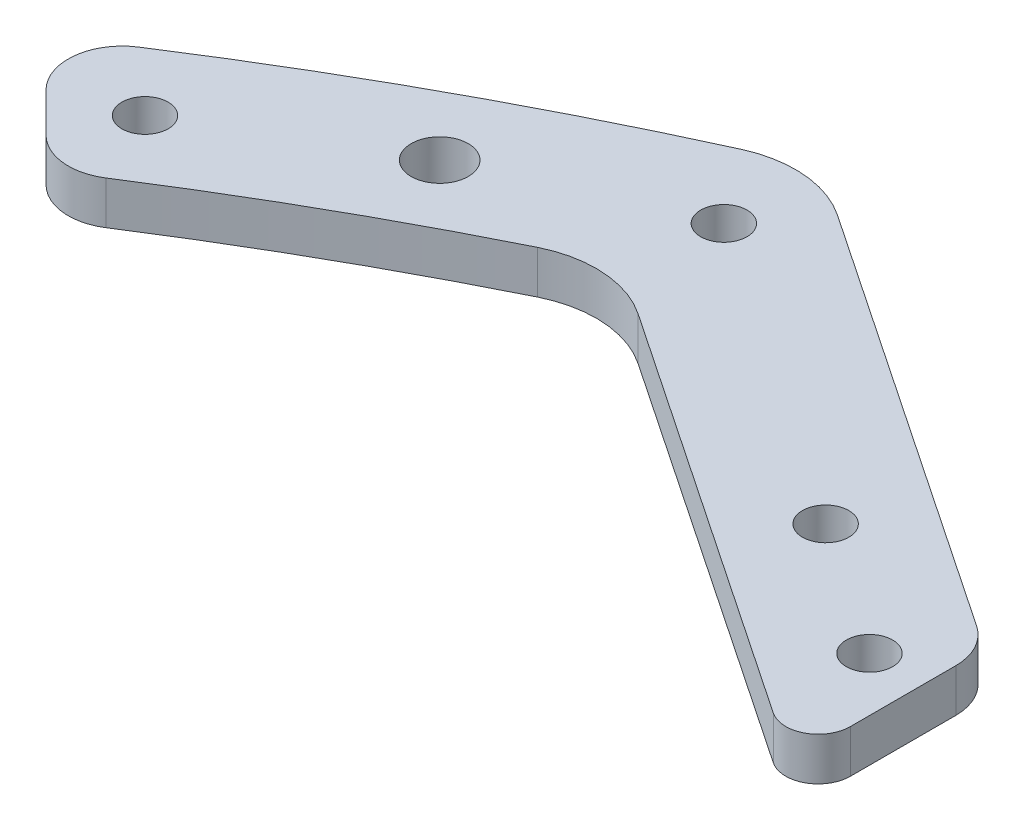
SolidWorks part; units mm, degrees
material "A-玻璃纤维"
ref_plane "前视基准面" through (0, 0, 0) normal (0, 0, 1) x (1, 0, 0)
ref_plane "上视基准面" through (0, 0, 0) normal (0, 1, 0) x (1, 0, 0)
ref_plane "右视基准面" through (0, 0, 0) normal (1, 0, 0) x (0, 0, -1)
sketch "草图1" plane through (0, 0, 0) normal (0, 1, 0) x (1, 0, 0)
  line L0 (0, 0) -> (275, 0) construction
  line L1 (0, 0) -> (0, 275) construction
  line L2 (0, 0) -> (194.4544, 194.4544) construction
  circle A0 centre (0, 0) radius 255
  circle A1 centre (0, 0) radius 275
  dimension "D1" = 510
  dimension "D2" = 20
  dimension "D3" = 45
extrude "凸台-拉伸1" add sketch "草图1" along normal blind 10
sketch "草图2" plane through (0, 10, 0) normal (0, 1, 0) x (1, 0, 0)
  line L0 (0, 0) -> (275, 0) construction
  line L1 (164.7559, 164.7559) -> (217.7889, 111.7229) construction
  line L2 (164.7559, 164.7559) -> (111.7229, 217.7889) construction
  line L3 (0, 0) -> (164.7559, 164.7559) construction
  line L4 (111.7229, 217.7889) -> (121.6224, 227.6884) construction
  line L5 (217.7889, 111.7229) -> (227.6884, 121.6224) construction
  line L6 (0, 0) -> (240.1716, 111.9938) construction
  line L7 (0, 0) -> (111.9938, 240.1716) construction
  line L8 (0, 0) -> (0, 275) construction
  line L9 (0, 185) -> (30, 185)
  line L10 (-110.5251, 257.2629) -> (-25.4233, 200)
  line L11 (111.9938, 240.1716) -> (30, 185)
  line L12 (0, 200) -> (-25.4233, 200)
  line L13 (240.1716, 111.9938) -> (185, 30)
  line L14 (185, 0) -> (185, 30)
  line L15 (-111.9938, 240.1716) -> (-30, 185)
  line L16 (0, 200) -> (25.4233, 200)
  line L17 (110.5251, 257.2629) -> (25.4233, 200)
  line L18 (257.2629, 110.5251) -> (200, 25.4233)
  line L19 (200, 0) -> (200, 25.4233)
  line L20 (0, 185) -> (-30, 185)
  line L21 (0, 185) -> (-30, 185) construction
  line L22 (0, 200) -> (-30, 200) construction
  line L23 (200, 0) -> (200, -1.5596) construction
  line L24 (185, 0) -> (185, -1.5596) construction
  line L25 (-200, -25.4233) -> (-200, 25.4233)
  line L26 (-257.2629, 110.5251) -> (-200, 25.4233)
  line L27 (-185, -30) -> (-185, 30)
  line L28 (-240.1716, 111.9938) -> (-185, 30)
  line L29 (185, 0) -> (185, -30)
  line L30 (200, 0) -> (200, -25.4233)
  line L31 (257.2629, -110.5251) -> (200, -25.4233)
  line L32 (240.1716, -111.9938) -> (185, -30)
  line L33 (164.7559, -164.7559) -> (111.7229, -217.7889) construction
  line L34 (110.5251, -257.2629) -> (25.4233, -200)
  line L35 (111.9938, -240.1716) -> (30, -185)
  line L36 (0, -185) -> (-30, -185)
  line L37 (0, -200) -> (-25.4233, -200)
  line L38 (0, -200) -> (25.4233, -200)
  line L39 (0, -185) -> (30, -185)
  line L40 (-111.9938, -240.1716) -> (-30, -185)
  line L41 (-110.5251, -257.2629) -> (-25.4233, -200)
  line L42 (-240.1716, -111.9938) -> (-185, -30)
  line L43 (-257.2629, -110.5251) -> (-200, -25.4233)
  circle A0 centre (0, 0) radius 275 construction
  arc A2 (111.9938, 240.1716) -> (240.1716, 111.9938) centre (0, 0) cw
  arc A3 (110.5251, 257.2629) -> (257.2629, 110.5251) centre (0, 0) cw
  arc A4 (-110.5251, 257.2629) -> (-257.2629, 110.5251) centre (0, 0) ccw
  arc A5 (-111.9938, 240.1716) -> (-240.1716, 111.9938) centre (0, 0) ccw
  arc A6 (110.5251, -257.2629) -> (257.2629, -110.5251) centre (0, 0) ccw
  arc A7 (111.9938, -240.1716) -> (240.1716, -111.9938) centre (0, 0) ccw
  arc A8 (-111.9938, -240.1716) -> (-240.1716, -111.9938) centre (0, 0) cw
  arc A9 (-110.5251, -257.2629) -> (-257.2629, -110.5251) centre (0, 0) cw
  point P60 (-185, 0)
  point P61 (-200, 0)
  dimension "D5" = 14
  dimension "D7" = 265
  dimension "D1" = 233
  dimension "D3" = 75
  dimension "D4" = 75
  dimension "D6" = 14
  dimension "D8" = 15
  dimension "D9" = 20
  dimension "D10" = 30
  dimension "D11" = 185
extrude "凸台-拉伸2" add sketch "草图2" along normal blind 10 separate body
sketch "草图8" plane through (0, 20, 0) normal (0, 1, 0) x (1, 0, 0)
  line L0 (0, 0) -> (-187.3833, 187.3833) construction
  line L1 (-243.7881, 137.7221) -> (-232.755, 126.689) construction
  line L2 (-137.7221, 243.7881) -> (-126.689, 232.755) construction
  line L3 (0, 0) -> (0, 200) construction
  line L4 (25.4233, 200) -> (-25.4233, 200) construction
  line L5 (-75, 233.3589) -> (-75, 215.2794) construction
  line L6 (75, 233.3589) -> (75, 215.2794) construction
  line L7 (-30, 185) -> (-111.9938, 240.1716) construction
  line L8 (-25.4233, 200) -> (-110.5251, 257.2629) construction
  line L9 (0, 0) -> (214.4019, 0) construction
  line L10 (200, -25.4233) -> (200, 25.4233) construction
  line L11 (-27.7116, 192.5) -> (-110.5251, 248.2231) construction
  line L12 (-10, 192.5) -> (-27.7116, 192.5) construction
  line L13 (-110.5251, 257.2629) -> (-110.5251, 248.2231) construction
  line L14 (-257.2629, 110.5251) -> (-248.2231, 110.5251) construction
  line L15 (-192.5, 27.7116) -> (-248.2231, 110.5251) construction
  line L16 (-233.3589, 75) -> (-215.2794, 75) construction
  line L17 (233.3589, 75) -> (215.2794, 75) construction
  line L18 (192.5, 27.7116) -> (248.2231, 110.5251) construction
  line L19 (257.2629, 110.5251) -> (248.2231, 110.5251) construction
  line L20 (243.7881, 137.7221) -> (232.755, 126.689) construction
  line L21 (137.7221, 243.7881) -> (126.689, 232.755) construction
  line L22 (0, 0) -> (187.3833, 187.3833) construction
  line L23 (110.5251, 257.2629) -> (110.5251, 248.2231) construction
  line L24 (27.7116, 192.5) -> (110.5251, 248.2231) construction
  line L25 (75, 233.3589) -> (75, 215.2794) construction
  arc A0 (-111.9938, 240.1716) -> (-240.1716, 111.9938) centre (0, 0) ccw construction
  arc A1 (-110.5251, 257.2629) -> (-257.2629, 110.5251) centre (0, 0) ccw construction
  circle A2 centre (-10, 192.5) radius 2.65
  circle A3 centre (10, 192.5) radius 2.65
  circle A4 centre (-10, -192.5) radius 2.65
  circle A5 centre (10, -192.5) radius 2.65
  circle A6 centre (192.5, 10) radius 2.65
  circle A8 centre (192.5, -10) radius 2.65
  circle A9 centre (-192.5, 10) radius 2.65
  circle A10 centre (-192.5, -10) radius 2.65
  circle A11 centre (-110.5251, 248.2231) radius 2.15
  circle A12 centre (-27.7116, 192.5) radius 2.15
  circle A13 centre (-44.3049, 203.6652) radius 2.15
  circle A14 centre (-56.7499, 212.0391) radius 2.15
  circle A15 centre (-69.1949, 220.413) radius 2.15
  circle A16 centre (-81.6399, 228.787) radius 2.15
  arc A17 (-238.2716, 132.2055) -> (-128.8116, 240.1233) centre (0, 0) cw construction
  circle A18 centre (-146.077, 230.0286) radius 2.15
  circle A19 centre (-164.4155, 217.2997) radius 2.15
  circle A20 centre (-183.6389, 201.3166) radius 2.15
  circle A21 centre (-201.3166, 183.6389) radius 2.15
  circle A22 centre (-217.2997, 164.4155) radius 2.15
  circle A23 centre (-230.0286, 146.077) radius 2.15
  circle A24 centre (-128.8116, 240.1233) radius 2.65
  circle A25 centre (-240.1233, 128.8116) radius 2.65
  circle A26 centre (-228.787, 81.6399) radius 2.15
  circle A27 centre (-220.413, 69.1949) radius 2.15
  circle A28 centre (-212.0391, 56.7499) radius 2.15
  circle A29 centre (-203.6652, 44.3049) radius 2.15
  circle A30 centre (-192.5, 27.7116) radius 2.15
  circle A31 centre (-248.2231, 110.5251) radius 2.15
  circle A32 centre (192.5, 27.7116) radius 2.15
  circle A33 centre (248.2231, 110.5251) radius 2.15
  circle A34 centre (203.6652, 44.3049) radius 2.15
  circle A35 centre (212.0391, 56.7499) radius 2.15
  circle A36 centre (220.413, 69.1949) radius 2.15
  circle A37 centre (228.787, 81.6399) radius 2.15
  circle A38 centre (240.1233, 128.8116) radius 2.65
  circle A39 centre (230.0286, 146.077) radius 2.15
  arc A40 (238.2716, 132.2055) -> (128.8116, 240.1233) centre (0, 0) ccw construction
  circle A41 centre (128.8116, 240.1233) radius 2.65
  circle A42 centre (201.3166, 183.6389) radius 2.15
  circle A43 centre (183.6389, 201.3166) radius 2.15
  circle A44 centre (164.4155, 217.2997) radius 2.15
  circle A45 centre (146.077, 230.0286) radius 2.15
  circle A46 centre (81.6399, 228.787) radius 2.15
  circle A47 centre (69.1949, 220.413) radius 2.15
  circle A48 centre (56.7499, 212.0391) radius 2.15
  circle A49 centre (44.3049, 203.6652) radius 2.15
  circle A50 centre (110.5251, 248.2231) radius 2.15
  circle A51 centre (27.7116, 192.5) radius 2.15
  circle A52 centre (217.2997, 164.4155) radius 2.15
  dimension "D1" = 75
  dimension "D3" = 5.3
  dimension "D4" = 20
  dimension "D5" = 7.5
  dimension "D6" = 5.3
  dimension "D7" = 20
  dimension "D8" = 7.5
  dimension "D10" = 4.3
  dimension "D11" = 4.3
  dimension "D12" = 15
  dimension "D13" = 15
  dimension "D14" = 15
  dimension "D15" = 20
  dimension "D16" = 4.3
  dimension "D17" = 20
  dimension "D18" = 25
  dimension "D19" = 20
  dimension "D20" = 25
  dimension "D21" = 25
  dimension "D22" = 5.3
  dimension "D23" = 20
  dimension "D2" = 75
  dimension "D9" = 7.5
extrude "切除-拉伸1" cut sketch "草图8" against normal through all
sketch "草图9" plane through (0, 20, 0) normal (0, 1, 0) x (1, 0, 0)
  line L0 (-157.0498, 231.8089) -> (-146.2376, 220.9968)
  line L1 (-64.1949, 226.0885) -> (-64.1949, 208.0089)
  line L2 (-25.4233, 200) -> (-110.5251, 257.2629) construction
  line L3 (-30, 185) -> (-111.9938, 240.1716) construction
  line L4 (-64.1949, 226.0885) -> (-110.5251, 257.2629)
  line L5 (-64.1949, 208.0089) -> (-111.9938, 240.1716)
  line L6 (0, 0) -> (0, 266.3831) construction
  line L7 (0, 0) -> (-187.3833, 187.3833) construction
  arc A0 (-110.5251, 257.2629) -> (-257.2629, 110.5251) centre (0, 0) ccw construction
  arc A1 (-111.9938, 240.1716) -> (-240.1716, 111.9938) centre (0, 0) ccw construction
  arc A2 (-110.5251, 257.2629) -> (-157.0498, 231.8089) centre (0, 0) ccw
  arc A3 (-111.9938, 240.1716) -> (-146.2376, 220.9968) centre (0, 0) ccw
  circle A4 centre (-69.1949, 220.413) radius 2.15 construction
  circle A5 centre (-146.077, 230.0286) radius 2.15 construction
  dimension "D1" = 5
  dimension "D2" = 6.5
extrude "切除-拉伸2" cut sketch "草图9" against normal through all flip side to cut
sketch "草图10" plane through (76.3367, 0, -113.4487) normal (-0.5583, 0, 0.8297) x (0.8297, 0, 0.5583)
  line L0 (-226.9958, 20) -> (-226.9958, 10) construction
  line L2 (-322.4897, 4) -> (-131.5019, 4)
  line L3 (-322.4897, 4) -> (-322.4897, 16)
  line L4 (-322.4897, 16) -> (-131.5019, 16)
  line L5 (-131.5019, 4) -> (-131.5019, 16)
  line L6 (-322.4897, 4) -> (-131.5019, 16) construction
  line L7 (-322.4897, 16) -> (-131.5019, 4) construction
  line L8 (-169.3835, 20) -> (-226.9958, 20) construction
  dimension "D1" = 4
extrude "切除-拉伸3" cut sketch "草图10" against normal through all both and the other way through all
fillet "圆角1" radius 3 1 edges at (-64.1949, 18, -208.0089)
fillet "圆角2" radius 10 2 edges at (-110.5251, 18, -257.2629) (-111.9938, 18, -240.1716)
fillet "圆角3" radius 5 3 edges at (-157.0498, 18, -231.8089) (-146.2376, 18, -220.9968) (-64.1949, 18, -226.0885)
sketch "草图11" plane through (76.3367, 0, -113.4487) normal (-0.5583, 0, 0.8297) x (0.8297, 0, 0.5583)
  line L1 (447.6463, -9.0752) -> (-304.0938, -9.0752)
  line L2 (447.6463, -9.0752) -> (447.6463, 16)
  line L3 (447.6463, 16) -> (-304.0938, 16)
  line L4 (-304.0938, -9.0752) -> (-304.0938, 16)
  line L5 (447.6463, -9.0752) -> (-304.0938, 16) construction
  line L6 (447.6463, 16) -> (-304.0938, -9.0752) construction
  line L7 (-243.1329, 16) -> (-229.9507, 16) construction
extrude "切除-拉伸4" cut sketch "草图11" against normal through all both and the other way through all
